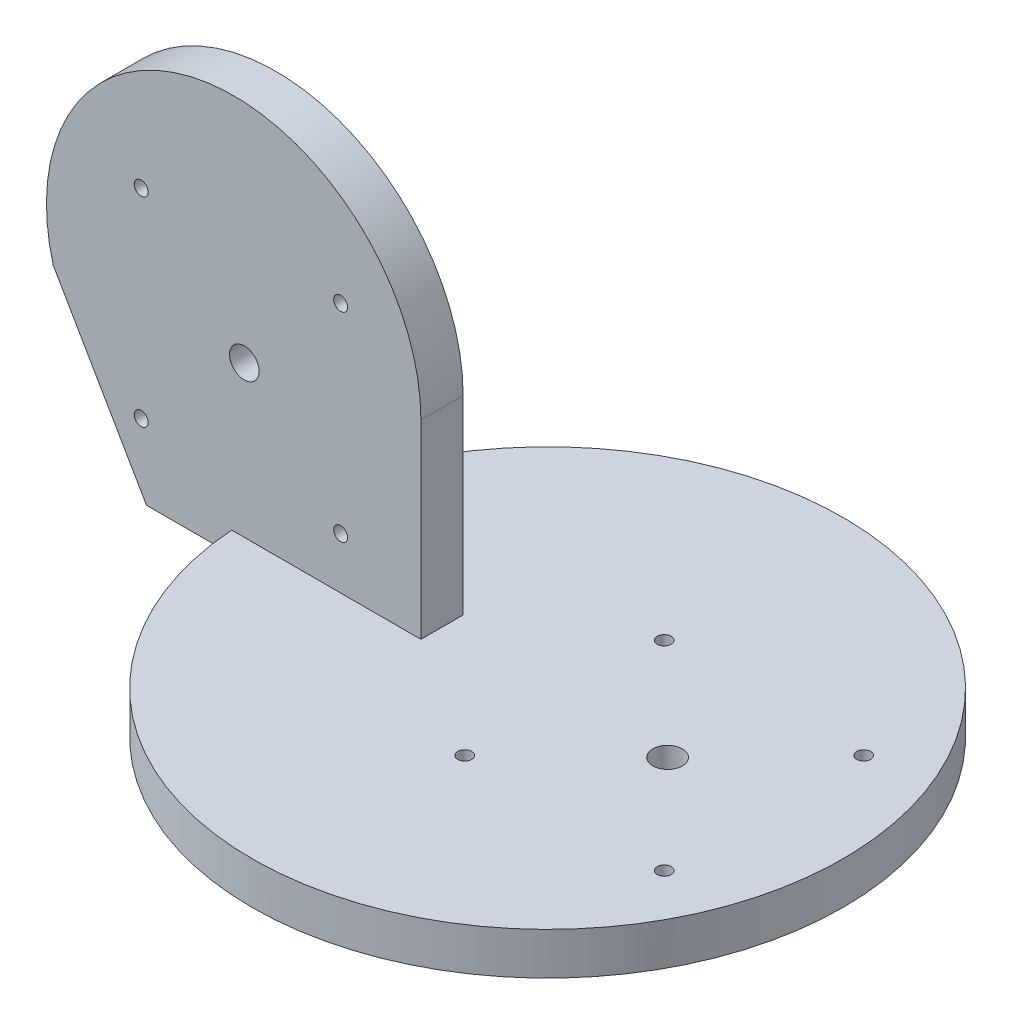
SolidWorks part; units mm, degrees
ref_plane "Front Plane" through (0, 0, 0) normal (0, 0, 1) x (1, 0, 0)
ref_plane "Top Plane" through (0, 0, 0) normal (0, 1, 0) x (1, 0, 0)
ref_plane "Right Plane" through (0, 0, 0) normal (1, 0, 0) x (0, 0, -1)
sketch "Sketch1" plane through (0, 0, 0) normal (0, 1, 0) x (1, 0, 0)
  circle A0 centre (0, 0) radius 70
  dimension "D1" = 140
extrude "Boss-Extrude1" add sketch "Sketch1" along normal blind 10
sketch "Sketch2" plane through (0, 0, 0) normal (0, -1, 0) x (1, 0, 0)
  circle A2 centre (0, 0) radius 65
  circle A3 centre (0, 0) radius 65
  dimension "D1" = 5
extrude "Boss-Extrude2" add sketch "Sketch2" along normal blind 3
sketch "Sketch3" plane through (0, 0, 0) normal (0, 0, 1) x (1, 0, 0)
  line L3 (-25, 55) -> (-25, 5)
  line L4 (-25, 5) -> (-90, 5)
  line L5 (-90, 5) -> (-112.0943, 43.2048)
  arc A2 (-112.0943, 43.2048) -> (-25, 55) centre (-69.3458, 55) cw
  dimension "D1" = 25
  dimension "D3" = 65
  dimension "D2" = 5
  dimension "D4" = 50
extrude "Boss-Extrude3" add sketch "Sketch3" along normal mid plane 10
hole_wizard "M4x0.7 Tapped Hole1" positions "Sketch4" profile "Sketch5" tap size "M4x0.7" standard "ANSI Metric"
sketch "Sketch4" plane through (0, 10, 0) normal (0, 1, 0) x (1, 0, 0)
  point P0 (4, 23.622)
  point P2 (51.244, 23.622)
  point P4 (51.244, -23.622)
  point P6 (4, -23.622)
  dimension "D1" = 47.244
  dimension "D2" = 47.244
  dimension "D3" = 4
  dimension "D4" = 23.622
sketch "Sketch5" plane through (4, 10, -23.622) normal (1, 0, 0) x (0, 0, 1)
  line L0 (0, 0) -> (0, 11.0914)
  line L1 (0, 11.0914) -> (1.65, 10.1)
  line L2 (1.65, 10.1) -> (1.65, 0)
  line L5 (1.65, 0) -> (0, 0)
  line L10 (0, 11.0914) -> (-1.65, 10.1) construction
  line L11 (0, -6.35) -> (0, 107.95) construction
  dimension "Tap Drill Dia." = 3.3
  dimension "Tap Drill Depth" = 10.1
  dimension "Drill Angle" = 118
cosmetic thread "Hole Thread1" parameters "D1"=8, "D2"=4
cosmetic thread "Hole Thread2" parameters "D1"=8, "D2"=4
cosmetic thread "Hole Thread3" parameters "D1"=8, "D2"=4
cosmetic thread "Hole Thread4" parameters "D1"=8, "D2"=4
hole_wizard "M8x1.0 Tapped Hole1" positions "Sketch6" profile "Sketch7" tap size "M8x1.0" standard "ANSI Metric" end condition through all
sketch "Sketch6" plane through (0, 10, 0) normal (0, 1, 0) x (1, 0, 0)
  point P0 (28.4268, 0)
  point P13 (0, 0)
cosmetic thread "Hole Thread5" parameters "D2"=8
sketch "Sketch7" plane through (28.4268, 10, 0) normal (1, 0, 0) x (0, 0, 1)
  line L0 (0, 0) -> (0, 13)
  line L1 (0, 13) -> (3.5, 13)
  line L2 (3.5, 13) -> (3.5, 0)
  line L5 (3.5, 0) -> (0, 0)
  line L11 (0, -6.35) -> (0, 107.95) construction
  dimension "Thru Tap Drill Dia." = 7
  dimension "Thru Tap Drill Depth" = 13
hole_wizard "M4x0.7 Tapped Hole3" positions "Sketch9" profile "Sketch11" tap size "M4x0.7" standard "ANSI Metric"
sketch "Sketch9" plane through (-95.2534, 45.7932, 5) normal (0, 0, 1) x (1, 0, 0)
  point P0 (4, 23.622)
  point P2 (51.244, 23.622)
  point P4 (51.244, -23.622)
  point P6 (4, -23.622)
  dimension "D1" = 47.244
  dimension "D2" = 47.244
sketch "Sketch11" plane through (-91.2534, 69.4152, 5) normal (1, 0, 0) x (0, -1, 0)
  line L0 (0, 0) -> (0, 11.0914)
  line L1 (0, 11.0914) -> (1.65, 10.1)
  line L2 (1.65, 10.1) -> (1.65, 0)
  line L5 (1.65, 0) -> (0, 0)
  line L10 (0, 11.0914) -> (-1.65, 10.1) construction
  line L11 (0, -6.35) -> (0, 107.95) construction
  dimension "Tap Drill Dia." = 3.3
  dimension "Tap Drill Depth" = 10.1
  dimension "Drill Angle" = 118
cosmetic thread "Hole Thread6" parameters "D1"=8, "D2"=4
cosmetic thread "Hole Thread7" parameters "D1"=8, "D2"=4
cosmetic thread "Hole Thread8" parameters "D1"=8, "D2"=4
cosmetic thread "Hole Thread9" parameters "D1"=8, "D2"=4
hole_wizard "M8x1.0 Tapped Hole2" positions "Sketch13" profile "Sketch15" tap size "M8x1.0" standard "ANSI Metric" end condition through all
sketch "Sketch13" plane through (-95.2534, 45.7932, 5) normal (0, 0, 1) x (1, 0, 0)
  point P0 (28.4268, 0)
  point P13 (0, 0)
cosmetic thread "Hole Thread10" parameters "D2"=8
sketch "Sketch15" plane through (-66.8266, 45.7932, 5) normal (1, 0, 0) x (0, -1, 0)
  line L0 (0, 0) -> (0, 75)
  line L1 (0, 75) -> (3.5, 75)
  line L2 (3.5, 75) -> (3.5, 0)
  line L5 (3.5, 0) -> (0, 0)
  line L11 (0, -6.35) -> (0, 107.95) construction
  dimension "Thru Tap Drill Dia." = 7
  dimension "Thru Tap Drill Depth" = 75
